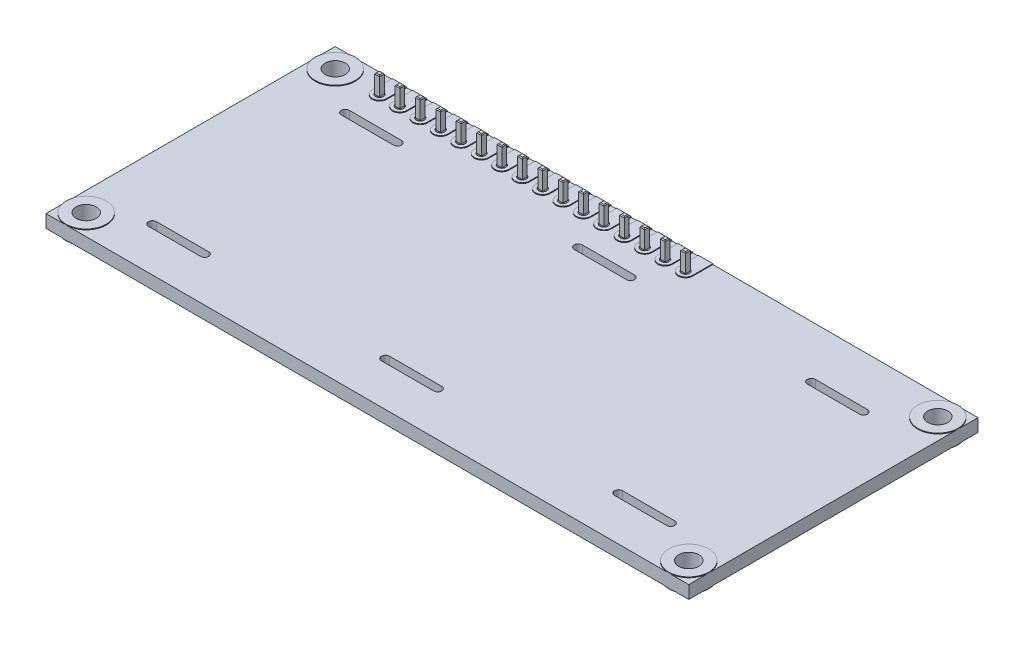
SolidWorks part; units mm, degrees
ref_plane "Front Plane" through (0, 0, 0) normal (0, 0, 1) x (1, 0, 0)
ref_plane "Top Plane" through (0, 0, 0) normal (0, 1, 0) x (1, 0, 0)
ref_plane "Right Plane" through (0, 0, 0) normal (1, 0, 0) x (0, 0, -1)
sketch "Sketch1" plane through (0, 0, 0) normal (0, 1, 0) x (1, 0, 0)
  line L0 (-32, 15.5) -> (-29.46, 15.5) construction
  line L1 (40, 18) -> (-40, 18)
  line L2 (40, 18) -> (40, -18)
  line L3 (40, -18) -> (-40, -18)
  line L4 (-40, 18) -> (-40, -18)
  line L5 (40, 18) -> (-40, -18) construction
  line L6 (40, -18) -> (-40, 18) construction
  line L7 (-37.5, 15.5) -> (37.5, 15.5) construction
  line L8 (-37.5, 15.5) -> (-37.5, -15.5) construction
  line L10 (37.5, 15.5) -> (37.5, -15.5) construction
  line L11 (-37.5, 15.5) -> (37.5, -15.5) construction
  line L12 (-37.5, -15.5) -> (37.5, 15.5) construction
  line L13 (0, 15.5) -> (0, -15.5) construction
  line L14 (-3.25, -12.5) -> (3.25, -12.5) construction
  line L15 (-3.25, -12) -> (3.25, -12)
  line L16 (-3.25, -13) -> (3.25, -13)
  line L17 (25.75, -12.5) -> (32.25, -12.5) construction
  line L18 (25.75, -12) -> (32.25, -12)
  line L19 (25.75, -13) -> (32.25, -13)
  line L20 (25.75, 11.5) -> (32.25, 11.5) construction
  line L21 (25.75, 12) -> (32.25, 12)
  line L22 (25.75, 11) -> (32.25, 11)
  line L23 (-3.25, 11.5) -> (3.25, 11.5) construction
  line L24 (-3.25, 12) -> (3.25, 12)
  line L25 (-3.25, 11) -> (3.25, 11)
  line L26 (-32.25, -12.5) -> (-25.75, -12.5) construction
  line L27 (-32.25, -12) -> (-25.75, -12)
  line L28 (-32.25, -13) -> (-25.75, -13)
  line L29 (-32.25, 11.5) -> (-25.75, 11.5) construction
  line L30 (-32.25, 12) -> (-25.75, 12)
  line L31 (-32.25, 11) -> (-25.75, 11)
  circle A0 centre (-37.5, 15.5) radius 1.25
  circle A1 centre (-37.5, -15.5) radius 1.25
  circle A2 centre (37.5, 15.5) radius 1.25
  circle A3 centre (37.5, -15.5) radius 1.25
  circle A4 centre (-32, 15.5) radius 0.5
  circle A5 centre (-29.46, 15.5) radius 0.5
  circle A6 centre (-26.92, 15.5) radius 0.5
  circle A7 centre (-24.38, 15.5) radius 0.5
  circle A8 centre (-21.84, 15.5) radius 0.5
  circle A9 centre (-19.3, 15.5) radius 0.5
  circle A10 centre (-16.76, 15.5) radius 0.5
  circle A11 centre (-14.22, 15.5) radius 0.5
  circle A12 centre (-11.68, 15.5) radius 0.5
  circle A13 centre (-9.14, 15.5) radius 0.5
  circle A14 centre (-6.6, 15.5) radius 0.5
  circle A15 centre (-4.06, 15.5) radius 0.5
  circle A16 centre (-1.52, 15.5) radius 0.5
  circle A17 centre (1.02, 15.5) radius 0.5
  circle A18 centre (3.56, 15.5) radius 0.5
  circle A19 centre (6.1, 15.5) radius 0.5
  arc A20 (-3.25, -12) -> (-3.25, -13) centre (-3.25, -12.5) ccw
  arc A21 (3.25, -13) -> (3.25, -12) centre (3.25, -12.5) ccw
  arc A22 (25.75, -12) -> (25.75, -13) centre (25.75, -12.5) ccw
  arc A23 (32.25, -13) -> (32.25, -12) centre (32.25, -12.5) ccw
  arc A24 (25.75, 12) -> (25.75, 11) centre (25.75, 11.5) ccw
  arc A25 (32.25, 11) -> (32.25, 12) centre (32.25, 11.5) ccw
  arc A26 (-3.25, 12) -> (-3.25, 11) centre (-3.25, 11.5) ccw
  arc A27 (3.25, 11) -> (3.25, 12) centre (3.25, 11.5) ccw
  arc A28 (-32.25, -12) -> (-32.25, -13) centre (-32.25, -12.5) ccw
  arc A29 (-25.75, -13) -> (-25.75, -12) centre (-25.75, -12.5) ccw
  arc A30 (-32.25, 12) -> (-32.25, 11) centre (-32.25, 11.5) ccw
  arc A31 (-25.75, 11) -> (-25.75, 12) centre (-25.75, 11.5) ccw
  point P0 (0, 0)
  point P6 (0, 0)
  point P51 (-29, 0)
  point P52 (0, -12.5)
  point P55 (0, -12.5)
  point P60 (-29, 0)
  point P62 (29, -12.5)
  point P65 (29, -12.5)
  point P70 (29, 11.5)
  point P73 (29, 11.5)
  point P78 (0, 11.5)
  point P81 (0, 11.5)
  point P86 (-29, -12.5)
  point P89 (-29, -12.5)
  point P94 (-29, 11.5)
  point P97 (-29, 11.5)
  dimension "D5" = 2.5
  dimension "D6" = 1
  dimension "D1" = 36
  dimension "D2" = 80
  dimension "D3" = 2.5
  dimension "D4" = 2.5
  dimension "D7" = 8
  dimension "D9" = 2.54
  dimension "D10" = 1
  dimension "D11" = 6.5
  dimension "D12" = 5
  dimension "D8" = 16
  dimension "D13" = 2
  dimension "D14" = 2
  dimension "D15" = 2
extrude "Boss-Extrude1" add sketch "Sketch1" against normal blind 1.6
sketch "Sketch2" plane through (0, 0, 0) normal (0, 1, 0) x (1, 0, 0)
  line L0 (-32.9, 15.5) -> (-32.9, 18)
  line L1 (40, 18) -> (-40, 18) construction
  line L2 (-32.9, 18) -> (-31.1, 18)
  line L3 (-31.1, 18) -> (-31.1, 15.5)
  arc A0 (-31.1, 15.5) -> (-32.9, 15.5) centre (-32, 15.5) cw
  circle A1 centre (-32, 15.5) radius 0.5 construction
  circle A2 centre (-32, 15.5) radius 0.5
  dimension "D1" = 1.8
extrude "Boss-Extrude2" add sketch "Sketch2" along normal blind 0.1
pattern_linear "LPattern1" count 16 spacing 2.54 along (1, 0, 0) of "Boss-Extrude2"
sketch "Sketch3" plane through (0, 0, 0) normal (0, 1, 0) x (1, 0, 0)
  circle A0 centre (-37.5, 15.5) radius 1.25 construction
  circle A1 centre (-37.5, -15.5) radius 1.25 construction
  circle A2 centre (37.5, 15.5) radius 1.25 construction
  circle A3 centre (37.5, -15.5) radius 1.25 construction
  circle A4 centre (-37.5, 15.5) radius 1.25
  circle A5 centre (-37.5, -15.5) radius 1.25
  circle A6 centre (37.5, 15.5) radius 1.25
  circle A7 centre (37.5, -15.5) radius 1.25
  circle A8 centre (-37.5, 15.5) radius 2.5
  circle A9 centre (-37.5, -15.5) radius 2.5
  circle A10 centre (37.5, -15.5) radius 2.5
  circle A11 centre (37.5, 15.5) radius 2.5
  dimension "D1" = 1.25
extrude "Boss-Extrude3" add sketch "Sketch3" along normal blind 0.1
sketch "Sketch4" plane through (0, -1.6, 0) normal (0, -1, 0) x (1, 0, 0)
  circle A0 centre (37.5, -15.5) radius 1.25 construction
  circle A1 centre (37.5, 15.5) radius 1.25 construction
  circle A2 centre (-37.5, 15.5) radius 1.25 construction
  circle A3 centre (-37.5, -15.5) radius 1.25 construction
  circle A4 centre (37.5, -15.5) radius 1.25
  circle A5 centre (37.5, 15.5) radius 1.25
  circle A6 centre (-37.5, 15.5) radius 1.25
  circle A7 centre (-37.5, -15.5) radius 1.25
  circle A8 centre (37.5, -15.5) radius 2.5
  circle A9 centre (37.5, 15.5) radius 2.5
  circle A10 centre (-37.5, 15.5) radius 2.5
  circle A11 centre (-37.5, -15.5) radius 2.5
  dimension "D1" = 1.25
extrude "Boss-Extrude4" add sketch "Sketch4" along normal blind 0.1
sketch "Sketch5" plane through (0, 0.1, 0) normal (0, 1, 0) x (1, 0, 0)
  line L1 (-32.3, 15.8) -> (-31.7, 15.8)
  line L2 (-32.3, 15.8) -> (-32.3, 15.2)
  line L3 (-32.3, 15.2) -> (-31.7, 15.2)
  line L4 (-31.7, 15.8) -> (-31.7, 15.2)
  line L5 (-32.3, 15.8) -> (-31.7, 15.2) construction
  line L6 (-32.3, 15.2) -> (-31.7, 15.8) construction
  point P0 (-32, 15.5)
  dimension "D1" = 0.6
extrude "Boss-Extrude5" add sketch "Sketch5" along normal blind 2.2 separate body
sketch "Sketch6" plane through (0, 2.3, 0) normal (0, 1, 0) x (1, 0, 0)
  line L0 (-32.3, 15.8) -> (-32.3, 15.2) construction
  line L1 (-32.3, 15.2) -> (-31.7, 15.2) construction
  line L2 (-31.7, 15.2) -> (-31.7, 15.8) construction
  line L3 (-31.7, 15.8) -> (-32.3, 15.8) construction
  line L4 (-32.3, 15.8) -> (-32.3, 15.2)
  line L5 (-32.3, 15.2) -> (-31.7, 15.2)
  line L6 (-31.7, 15.2) -> (-31.7, 15.8)
  line L7 (-31.7, 15.8) -> (-32.3, 15.8)
extrude "Boss-Extrude6" add sketch "Sketch6" along normal blind 0.1 draft 45
sketch "Sketch7" plane through (0, 0.1, 0) normal (0, -1, 0) x (1, 0, 0)
  line L0 (-32.3, -15.2) -> (-31.7, -15.2) construction
  line L1 (-31.7, -15.2) -> (-31.7, -15.8) construction
  line L2 (-31.7, -15.8) -> (-32.3, -15.8) construction
  line L3 (-32.3, -15.8) -> (-32.3, -15.2) construction
  line L4 (-32.3, -15.2) -> (-31.7, -15.2)
  line L5 (-31.7, -15.2) -> (-31.7, -15.8)
  line L6 (-31.7, -15.8) -> (-32.3, -15.8)
  line L7 (-32.3, -15.8) -> (-32.3, -15.2)
extrude "Boss-Extrude7" add sketch "Sketch7" along normal blind 0.1 draft 45
pattern_linear "LPattern2" count 16 spacing 2.54 along (1, 0, 0) of "Boss-Extrude5", "Boss-Extrude6", "Boss-Extrude7"
sketch "Sketch8" plane through (0, -1.6, 0) normal (0, -1, 0) x (1, 0, 0)
  line L1 (-33.25, -14.25) -> (7.25, -14.25)
  line L2 (-33.25, -14.25) -> (-33.25, -16.75)
  line L3 (-33.25, -16.75) -> (7.25, -16.75)
  line L4 (7.25, -14.25) -> (7.25, -16.75)
  circle A0 centre (-32, -15.5) radius 0.5 construction
  dimension "D4" = 1.25
  dimension "D1" = 2.5
  dimension "D2" = 40.5
  dimension "D3" = 1.25
extrude "Boss-Extrude8" add sketch "Sketch8" along normal blind 9
sketch "Sketch9" plane through (0, -10.6, 0) normal (0, -1, 0) x (1, 0, 0)
  line L0 (-33.25, -15.5) -> (-27.3638, -15.5) construction
  line L1 (-33.25, -14.25) -> (-33.25, -16.75) construction
  line L3 (-32.25, -15) -> (-31.25, -15)
  line L4 (-32.25, -15) -> (-32.25, -16)
  line L5 (-32.25, -16) -> (-31.25, -16)
  line L6 (-31.25, -15) -> (-31.25, -16)
  line L7 (-32.25, -15) -> (-31.25, -16) construction
  line L8 (-32.25, -16) -> (-31.25, -15) construction
  point P4 (-31.75, -15.5)
  dimension "D1" = 1
  dimension "D2" = 1
extrude "Cut-Extrude1" cut sketch "Sketch9" against normal blind 8
chamfer "Chamfer1" distance 0.375 angle 45 4 edges at (-31.75, -10.6, -16) (-31.25, -10.6, -15.5) (-31.75, -10.6, -15) (-32.25, -10.6, -15.5)
pattern_linear "LPattern3" count 16 spacing 2.5 along (1, 0, 0) of "Cut-Extrude1", "Chamfer1"
